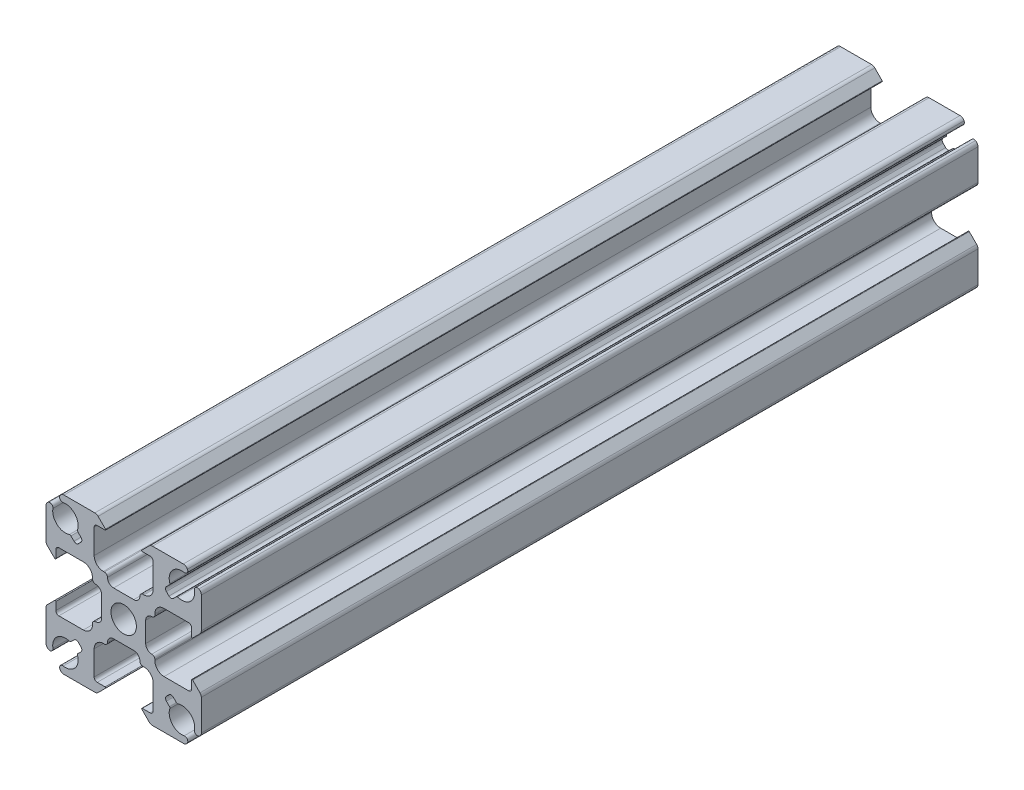
SolidWorks part; units mm, degrees
ref_plane "Front Plane" through (0, 0, 0) normal (0, 0, 1) x (1, 0, 0)
ref_plane "Top Plane" through (0, 0, 0) normal (0, 1, 0) x (1, 0, 0)
ref_plane "Right Plane" through (0, 0, 0) normal (1, 0, 0) x (0, 0, -1)
ref_plane "Plane1" through (0, 0, 0) normal (0, 0, -1) x (-1, 0, 0)
sketch "Sketch1" plane through (0, 0, 0) normal (0, 0, -1) x (-1, 0, 0)
  line L0 (-7.4885, 8.6199) -> (-6.9856, 8.117)
  line L1 (-6.9856, 7.4099) -> (-7.4099, 6.9856)
  line L2 (-8.117, 6.9856) -> (-8.6199, 7.4885)
  line L3 (-12.7, 9.7594) -> (-12.7, 4.7107)
  line L4 (-12.4803, 4.1803) -> (-11.2707, 2.9707)
  line L5 (-11.1, 3.0414) -> (-11.1, 4.325)
  line L6 (-10.6, 4.825) -> (-6.6, 4.825)
  line L7 (-5.1, 3.325) -> (-5.1, 3.15)
  line L8 (-3.6, 1.65) -> (-3.6, -1.65)
  line L9 (-5.1, -3.15) -> (-5.1, -3.325)
  line L10 (-6.6, -4.825) -> (-10.6, -4.825)
  line L11 (-11.1, -4.325) -> (-11.1, -3.0414)
  line L12 (-11.2707, -2.9707) -> (-12.4803, -4.1803)
  line L13 (-12.7, -4.7107) -> (-12.7, -9.7594)
  line L14 (-8.6199, -7.4885) -> (-8.117, -6.9856)
  line L15 (-7.4099, -6.9856) -> (-6.9856, -7.4099)
  line L16 (-6.9856, -8.117) -> (-7.4885, -8.6199)
  line L17 (-9.7594, -12.7) -> (-4.7107, -12.7)
  line L18 (-4.1803, -12.4803) -> (-2.9707, -11.2707)
  line L19 (-3.0414, -11.1) -> (-4.325, -11.1)
  line L20 (-4.825, -10.6) -> (-4.825, -6.6)
  line L21 (-3.325, -5.1) -> (-3.15, -5.1)
  line L22 (-1.65, -3.6) -> (1.65, -3.6)
  line L23 (3.15, -5.1) -> (3.325, -5.1)
  line L24 (4.825, -6.6) -> (4.825, -10.6)
  line L25 (4.325, -11.1) -> (3.0414, -11.1)
  line L26 (2.9707, -11.2707) -> (4.1803, -12.4803)
  line L27 (4.7107, -12.7) -> (9.7594, -12.7)
  line L28 (7.4885, -8.6199) -> (6.9856, -8.117)
  line L29 (6.9856, -7.4099) -> (7.4099, -6.9856)
  line L30 (8.117, -6.9856) -> (8.6199, -7.4885)
  line L31 (12.7, -9.7594) -> (12.7, -4.7107)
  line L32 (12.4803, -4.1803) -> (11.2707, -2.9707)
  line L33 (11.1, -3.0414) -> (11.1, -4.325)
  line L34 (10.6, -4.825) -> (6.6, -4.825)
  line L35 (5.1, -3.325) -> (5.1, -3.15)
  line L36 (3.6, -1.65) -> (3.6, 1.65)
  line L37 (5.1, 3.15) -> (5.1, 3.325)
  line L38 (6.6, 4.825) -> (10.6, 4.825)
  line L39 (11.1, 4.325) -> (11.1, 3.0414)
  line L40 (11.2707, 2.9707) -> (12.4803, 4.1803)
  line L41 (12.7, 4.7107) -> (12.7, 9.7594)
  line L42 (8.6199, 7.4885) -> (8.117, 6.9856)
  line L43 (7.4099, 6.9856) -> (6.9856, 7.4099)
  line L44 (6.9856, 8.117) -> (7.4885, 8.6199)
  line L45 (9.7594, 12.7) -> (4.7107, 12.7)
  line L46 (4.1803, 12.4803) -> (2.9707, 11.2707)
  line L47 (3.0414, 11.1) -> (4.325, 11.1)
  line L48 (4.825, 10.6) -> (4.825, 6.6)
  line L49 (3.325, 5.1) -> (3.15, 5.1)
  line L50 (1.65, 3.6) -> (-1.65, 3.6)
  line L51 (-3.15, 5.1) -> (-3.325, 5.1)
  line L52 (-4.825, 6.6) -> (-4.825, 10.6)
  line L53 (-4.325, 11.1) -> (-3.0414, 11.1)
  line L54 (-2.9707, 11.2707) -> (-4.1803, 12.4803)
  line L55 (-4.7107, 12.7) -> (-9.7594, 12.7)
  circle A0 centre (0, 0) radius 2.08
  arc A1 (-9.7594, 12.7) -> (-10.4266, 12.2927) centre (-9.7594, 11.95) ccw
  arc A2 (-10.4266, 12.2927) -> (-9.8933, 11.5721) centre (-9.9818, 12.0642) ccw
  arc A3 (-9.8933, 11.5721) -> (-7.5492, 8.8748) centre (-9.525, 9.525) cw
  arc A4 (-7.5492, 8.8748) -> (-7.4885, 8.6199) centre (-7.3118, 8.7967) ccw
  arc A5 (-6.9856, 8.117) -> (-6.9856, 7.4099) centre (-7.3392, 7.7635) cw
  arc A6 (-7.4099, 6.9856) -> (-8.117, 6.9856) centre (-7.7635, 7.3392) cw
  arc A7 (-8.6199, 7.4885) -> (-8.8748, 7.5492) centre (-8.7967, 7.3118) ccw
  arc A8 (-8.8748, 7.5492) -> (-11.5721, 9.8933) centre (-9.525, 9.525) cw
  arc A9 (-11.5721, 9.8933) -> (-12.2927, 10.4266) centre (-12.0642, 9.9818) ccw
  arc A10 (-12.2927, 10.4266) -> (-12.7, 9.7594) centre (-11.95, 9.7594) ccw
  arc A11 (-12.7, 4.7107) -> (-12.4803, 4.1803) centre (-11.95, 4.7107) ccw
  arc A12 (-11.2707, 2.9707) -> (-11.1, 3.0414) centre (-11.2, 3.0414) ccw
  arc A13 (-11.1, 4.325) -> (-10.6, 4.825) centre (-10.6, 4.325) cw
  arc A14 (-6.6, 4.825) -> (-5.1, 3.325) centre (-6.6, 3.325) cw
  arc A15 (-5.1, 3.15) -> (-4.6, 2.65) centre (-4.6, 3.15) ccw
  arc A16 (-4.6, 2.65) -> (-3.6, 1.65) centre (-4.6, 1.65) cw
  arc A17 (-3.6, -1.65) -> (-4.6, -2.65) centre (-4.6, -1.65) cw
  arc A18 (-4.6, -2.65) -> (-5.1, -3.15) centre (-4.6, -3.15) ccw
  arc A19 (-5.1, -3.325) -> (-6.6, -4.825) centre (-6.6, -3.325) cw
  arc A20 (-10.6, -4.825) -> (-11.1, -4.325) centre (-10.6, -4.325) cw
  arc A21 (-11.1, -3.0414) -> (-11.2707, -2.9707) centre (-11.2, -3.0414) ccw
  arc A22 (-12.4803, -4.1803) -> (-12.7, -4.7107) centre (-11.95, -4.7107) ccw
  arc A23 (-12.7, -9.7594) -> (-12.2927, -10.4266) centre (-11.95, -9.7594) ccw
  arc A24 (-12.2927, -10.4266) -> (-11.5721, -9.8933) centre (-12.0642, -9.9818) ccw
  arc A25 (-11.5721, -9.8933) -> (-8.8748, -7.5492) centre (-9.525, -9.525) cw
  arc A26 (-8.8748, -7.5492) -> (-8.6199, -7.4885) centre (-8.7967, -7.3118) ccw
  arc A27 (-8.117, -6.9856) -> (-7.4099, -6.9856) centre (-7.7635, -7.3392) cw
  arc A28 (-6.9856, -7.4099) -> (-6.9856, -8.117) centre (-7.3392, -7.7635) cw
  arc A29 (-7.4885, -8.6199) -> (-7.5492, -8.8748) centre (-7.3118, -8.7967) ccw
  arc A30 (-7.5492, -8.8748) -> (-9.8933, -11.5721) centre (-9.525, -9.525) cw
  arc A31 (-9.8933, -11.5721) -> (-10.4266, -12.2927) centre (-9.9818, -12.0642) ccw
  arc A32 (-10.4266, -12.2927) -> (-9.7594, -12.7) centre (-9.7594, -11.95) ccw
  arc A33 (-4.7107, -12.7) -> (-4.1803, -12.4803) centre (-4.7107, -11.95) ccw
  arc A34 (-2.9707, -11.2707) -> (-3.0414, -11.1) centre (-3.0414, -11.2) ccw
  arc A35 (-4.325, -11.1) -> (-4.825, -10.6) centre (-4.325, -10.6) cw
  arc A36 (-4.825, -6.6) -> (-3.325, -5.1) centre (-3.325, -6.6) cw
  arc A37 (-3.15, -5.1) -> (-2.65, -4.6) centre (-3.15, -4.6) ccw
  arc A38 (-2.65, -4.6) -> (-1.65, -3.6) centre (-1.65, -4.6) cw
  arc A39 (1.65, -3.6) -> (2.65, -4.6) centre (1.65, -4.6) cw
  arc A40 (2.65, -4.6) -> (3.15, -5.1) centre (3.15, -4.6) ccw
  arc A41 (3.325, -5.1) -> (4.825, -6.6) centre (3.325, -6.6) cw
  arc A42 (4.825, -10.6) -> (4.325, -11.1) centre (4.325, -10.6) cw
  arc A43 (3.0414, -11.1) -> (2.9707, -11.2707) centre (3.0414, -11.2) ccw
  arc A44 (4.1803, -12.4803) -> (4.7107, -12.7) centre (4.7107, -11.95) ccw
  arc A45 (9.7594, -12.7) -> (10.4266, -12.2927) centre (9.7594, -11.95) ccw
  arc A46 (10.4266, -12.2927) -> (9.8933, -11.5721) centre (9.9818, -12.0642) ccw
  arc A47 (9.8933, -11.5721) -> (7.5492, -8.8748) centre (9.525, -9.525) cw
  arc A48 (7.5492, -8.8748) -> (7.4885, -8.6199) centre (7.3118, -8.7967) ccw
  arc A49 (6.9856, -8.117) -> (6.9856, -7.4099) centre (7.3392, -7.7635) cw
  arc A50 (7.4099, -6.9856) -> (8.117, -6.9856) centre (7.7635, -7.3392) cw
  arc A51 (8.6199, -7.4885) -> (8.8748, -7.5492) centre (8.7967, -7.3118) ccw
  arc A52 (8.8748, -7.5492) -> (11.5721, -9.8933) centre (9.525, -9.525) cw
  arc A53 (11.5721, -9.8933) -> (12.2927, -10.4266) centre (12.0642, -9.9818) ccw
  arc A54 (12.2927, -10.4266) -> (12.7, -9.7594) centre (11.95, -9.7594) ccw
  arc A55 (12.7, -4.7107) -> (12.4803, -4.1803) centre (11.95, -4.7107) ccw
  arc A56 (11.2707, -2.9707) -> (11.1, -3.0414) centre (11.2, -3.0414) ccw
  arc A57 (11.1, -4.325) -> (10.6, -4.825) centre (10.6, -4.325) cw
  arc A58 (6.6, -4.825) -> (5.1, -3.325) centre (6.6, -3.325) cw
  arc A59 (5.1, -3.15) -> (4.6, -2.65) centre (4.6, -3.15) ccw
  arc A60 (4.6, -2.65) -> (3.6, -1.65) centre (4.6, -1.65) cw
  arc A61 (3.6, 1.65) -> (4.6, 2.65) centre (4.6, 1.65) cw
  arc A62 (4.6, 2.65) -> (5.1, 3.15) centre (4.6, 3.15) ccw
  arc A63 (5.1, 3.325) -> (6.6, 4.825) centre (6.6, 3.325) cw
  arc A64 (10.6, 4.825) -> (11.1, 4.325) centre (10.6, 4.325) cw
  arc A65 (11.1, 3.0414) -> (11.2707, 2.9707) centre (11.2, 3.0414) ccw
  arc A66 (12.4803, 4.1803) -> (12.7, 4.7107) centre (11.95, 4.7107) ccw
  arc A67 (12.7, 9.7594) -> (12.2927, 10.4266) centre (11.95, 9.7594) ccw
  arc A68 (12.2927, 10.4266) -> (11.5721, 9.8933) centre (12.0642, 9.9818) ccw
  arc A69 (11.5721, 9.8933) -> (8.8748, 7.5492) centre (9.525, 9.525) cw
  arc A70 (8.8748, 7.5492) -> (8.6199, 7.4885) centre (8.7967, 7.3118) ccw
  arc A71 (8.117, 6.9856) -> (7.4099, 6.9856) centre (7.7635, 7.3392) cw
  arc A72 (6.9856, 7.4099) -> (6.9856, 8.117) centre (7.3392, 7.7635) cw
  arc A73 (7.4885, 8.6199) -> (7.5492, 8.8748) centre (7.3118, 8.7967) ccw
  arc A74 (7.5492, 8.8748) -> (9.8933, 11.5721) centre (9.525, 9.525) cw
  arc A75 (9.8933, 11.5721) -> (10.4266, 12.2927) centre (9.9818, 12.0642) ccw
  arc A76 (10.4266, 12.2927) -> (9.7594, 12.7) centre (9.7594, 11.95) ccw
  arc A77 (4.7107, 12.7) -> (4.1803, 12.4803) centre (4.7107, 11.95) ccw
  arc A78 (2.9707, 11.2707) -> (3.0414, 11.1) centre (3.0414, 11.2) ccw
  arc A79 (4.325, 11.1) -> (4.825, 10.6) centre (4.325, 10.6) cw
  arc A80 (4.825, 6.6) -> (3.325, 5.1) centre (3.325, 6.6) cw
  arc A81 (3.15, 5.1) -> (2.65, 4.6) centre (3.15, 4.6) ccw
  arc A82 (2.65, 4.6) -> (1.65, 3.6) centre (1.65, 4.6) cw
  arc A83 (-1.65, 3.6) -> (-2.65, 4.6) centre (-1.65, 4.6) cw
  arc A84 (-2.65, 4.6) -> (-3.15, 5.1) centre (-3.15, 4.6) ccw
  arc A85 (-3.325, 5.1) -> (-4.825, 6.6) centre (-3.325, 6.6) cw
  arc A86 (-4.825, 10.6) -> (-4.325, 11.1) centre (-4.325, 10.6) cw
  arc A87 (-3.0414, 11.1) -> (-2.9707, 11.2707) centre (-3.0414, 11.2) ccw
  arc A88 (-4.1803, 12.4803) -> (-4.7107, 12.7) centre (-4.7107, 11.95) ccw
extrude "Boss-Extrude1" add sketch "Sketch1" against normal mid plane 127
hole_wizard "Tap Drill for M6x1.0 Tap1" positions "Sketch4" profile "Sketch3" hole size "M6x1.0" standard "ANSI Metric"
sketch "Sketch4" plane through (0, -3.6, 0) normal (0, -1, 0) x (-1, 0, 0)
  line L0 (-1.65, -63.5) -> (1.65, -63.5) construction
  point P0 (0, -50.8)
  dimension "D1" = 12.7
sketch "Sketch3" plane through (0, -3.6, 50.8) normal (1, 0, 0) x (0, 0, -1)
  line L0 (0, 0) -> (0, 16.3)
  line L1 (0, 16.3) -> (2.5, 16.3)
  line L2 (2.5, 16.3) -> (2.5, 0)
  line L5 (2.5, 0) -> (0, 0)
  line L11 (0, -6.35) -> (0, 107.95) construction
  dimension "Thru Hole Dia." = 5
  dimension "Thru Hole Depth" = 16.3
